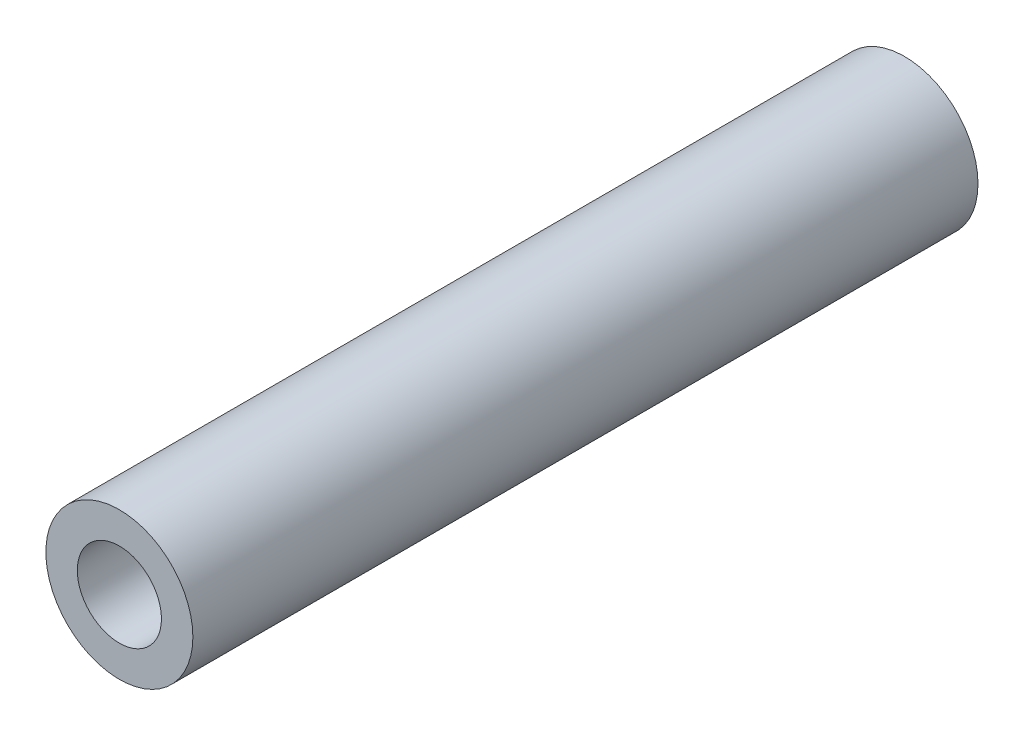
SolidWorks part; units mm, degrees
ref_plane "Front Plane" through (0, 0, 0) normal (0, 0, 1) x (1, 0, 0)
ref_plane "Top Plane" through (0, 0, 0) normal (0, 1, 0) x (1, 0, 0)
ref_plane "Right Plane" through (0, 0, 0) normal (1, 0, 0) x (0, 0, -1)
sketch "Sketch1" plane through (0, 0, 16.35) normal (0, 0, 1) x (1, 0, 0)
  circle A0 centre (1803.9912, -1743.8494) radius 4.63
  circle A1 centre (1803.9912, -1743.8494) radius 2.65
extrude "Boss-Extrude1" add sketch "Sketch1" along normal up to surface (49.45 mm away)
